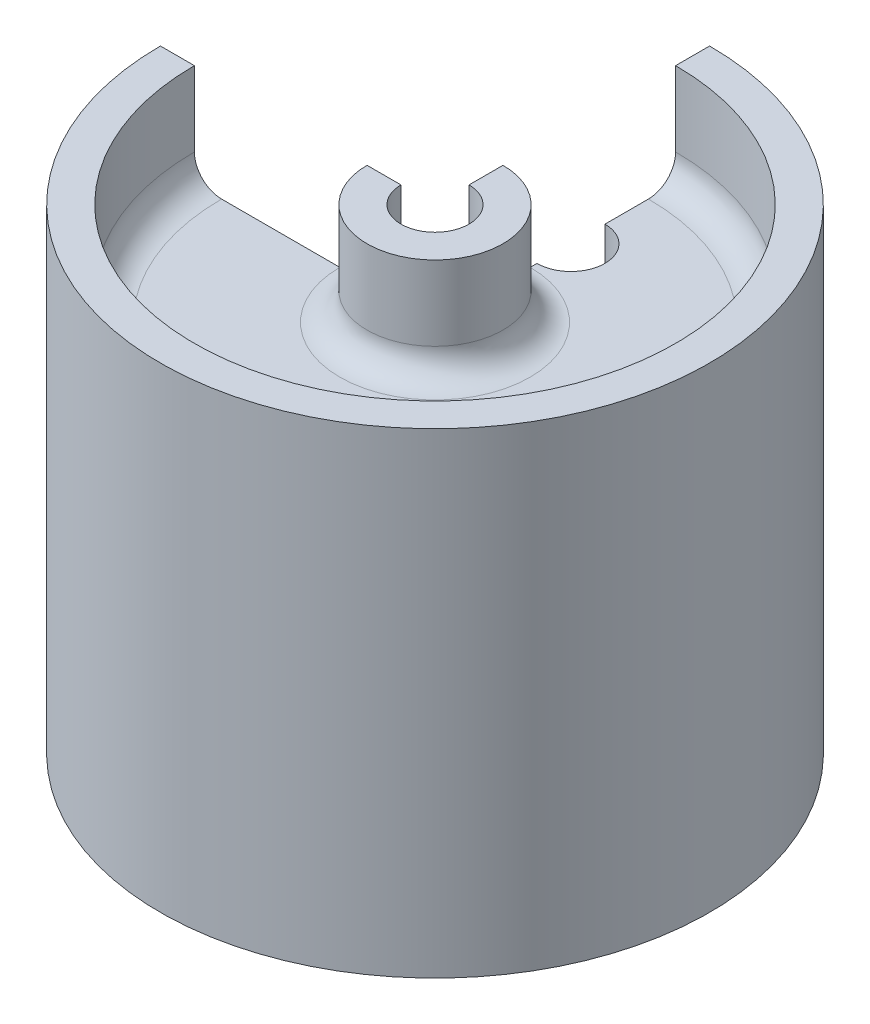
SolidWorks part; units mm, degrees
ref_plane "Front Plane" through (0, 0, 0) normal (0, 0, 1) x (1, 0, 0)
ref_plane "Top Plane" through (0, 0, 0) normal (0, 1, 0) x (1, 0, 0)
ref_plane "Right Plane" through (0, 0, 0) normal (1, 0, 0) x (0, 0, -1)
sketch "Sketch1" plane through (0, 0, 0) normal (1, 0, 0) x (0, 0, -1)
  line L3 (22.479, 35.4984) -> (22.479, 45.0234)
  line L4 (22.479, 45.0234) -> (25.654, 45.0234)
  line L5 (25.654, 45.0234) -> (25.654, 0.5734)
  line L6 (25.654, 0.5734) -> (22.479, 0.5734)
  line L7 (22.479, 0.5734) -> (22.479, 32.3234)
  line L8 (22.479, 32.3234) -> (6.35, 32.3234)
  line L12 (0, 45.0234) -> (0, 0) construction
  line L13 (22.479, 35.4984) -> (6.35, 35.4984)
  line L14 (6.35, 35.4984) -> (6.35, 45.0234)
  line L15 (6.35, 45.0234) -> (3.175, 45.0234)
  line L16 (3.175, 45.0234) -> (3.175, 0.5734)
  line L17 (3.175, 0.5734) -> (6.35, 0.5734)
  line L19 (6.35, 32.3234) -> (6.35, 0.5734)
  point P13 (0, 0)
  dimension "D1" = 44.45
  dimension "D2" = 16.129
  dimension "D3" = 3.175
  dimension "D4" = 31.75
  dimension "D5" = 16.129
  dimension "D6" = 9.525
  dimension "D7" = 3.175
revolve "Revolve2" add sketch "Sketch1" angle 270 about L12
sketch "Sketch5" plane through (0, 0, 0) normal (0, 1, 0) x (1, 0, 0)
  circle A0 centre (0, 12.7) radius 3.175
  point P2 (0, 0)
  point P4 (0, 0)
  dimension "D1" = 6.35
  dimension "D2" = 12.7
extrude "Cut-Extrude1" cut sketch "Sketch5" along normal through all
fillet "Fillet1" radius 2.54 2 edges at (4.4901, 32.3234, 4.4901) (15.8951, 32.3234, 15.8951)
fillet "Fillet2" radius 2.54 2 edges at (15.8951, 35.4984, 15.8951) (4.4901, 35.4984, 4.4901)
